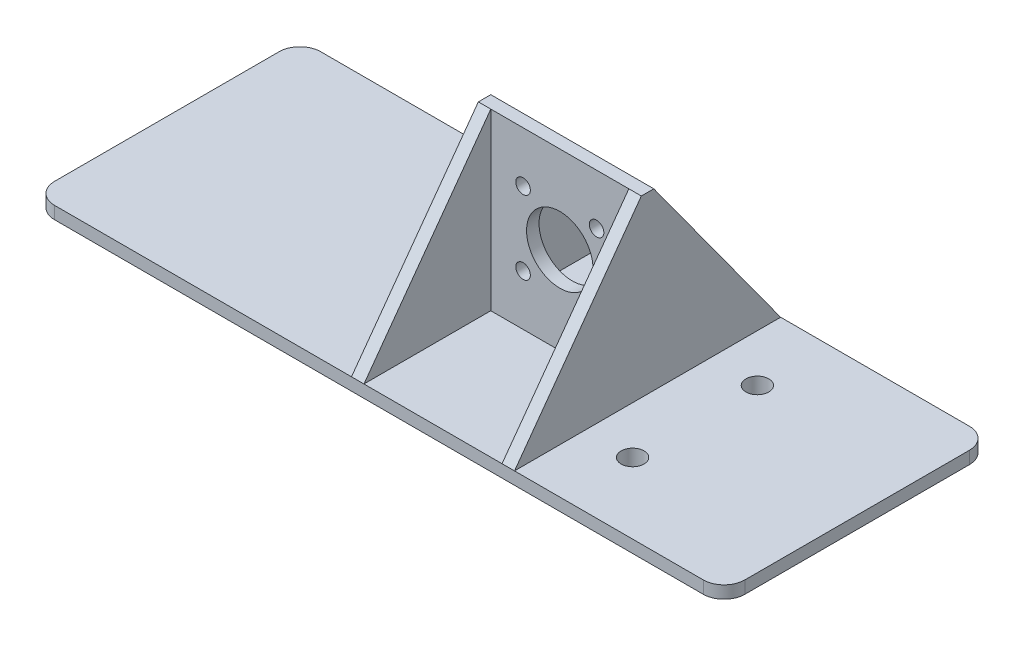
SolidWorks part; units mm, degrees
material "ABS PC"
ref_plane "Front Plane" through (0, 0, 0) normal (0, 0, 1) x (1, 0, 0)
ref_plane "Top Plane" through (0, 0, 0) normal (0, 1, 0) x (1, 0, 0)
ref_plane "Right Plane" through (0, 0, 0) normal (1, 0, 0) x (0, 0, -1)
sketch "Sketch1" plane through (0, 0, 0) normal (0, 1, 0) x (1, 0, 0)
  line L1 (78, 32) -> (-78, 32)
  line L2 (83, 27) -> (83, -27)
  line L3 (78, -32) -> (-78, -32)
  line L4 (-83, 27) -> (-83, -27)
  line L5 (83, 32) -> (-83, -32) construction
  line L6 (83, -32) -> (-83, 32) construction
  arc A0 (78, 32) -> (83, 27) centre (78, 27) cw
  arc A1 (83, -27) -> (78, -32) centre (78, -27) cw
  arc A2 (-78, -32) -> (-83, -27) centre (-78, -27) cw
  arc A3 (-78, 32) -> (-83, 27) centre (-78, 27) ccw
  point P0 (0, 0)
  dimension "D1" = 5
  dimension "D2" = 166
  dimension "D3" = 64
extrude "Boss-Extrude1" add sketch "Sketch1" along normal blind 3
sketch "Sketch2" plane through (0, 3, 0) normal (0, 1, 0) x (1, 0, 0)
  line L0 (-83, 0) -> (83, 0) construction
  line L1 (-83, 27) -> (-83, -27) construction
  line L2 (83, -27) -> (83, 27) construction
  circle A0 centre (44, -15) radius 2.75
  circle A1 centre (44, 15) radius 2.75
  circle A2 centre (-18, 0) radius 2.75
  dimension "D1" = 30
  dimension "D3" = 5.5
  dimension "D4" = 62
  dimension "D2" = 127
extrude "Cut-Extrude1" cut sketch "Sketch2" against normal through all
sketch "Sketch3" plane through (0, 3, 0) normal (0, 1, 0) x (1, 0, 0)
  line L0 (-78, -32) -> (78, -32) construction
  line L1 (-6.6, 32) -> (32.6, 32) construction
  line L2 (-6.6, 0) -> (-6.6, -32) construction
  line L3 (-6.6, -32) -> (32.6, -32) construction
  line L4 (32.6, -15) -> (32.6, -32) construction
  line L5 (78, 32) -> (-78, 32) construction
  line L6 (44, -15) -> (32.6, -15) construction
  line L7 (-18, 0) -> (-6.6, 0) construction
  line L8 (-6.6, 32) -> (-6.6, 0) construction
  line L9 (32.6, 32) -> (32.6, -15) construction
  line L11 (-6.6, 1.5) -> (32.6, 1.5)
  line L12 (-6.6, 1.5) -> (-6.6, -1.5)
  line L13 (-6.6, -1.5) -> (32.6, -1.5)
  line L14 (32.6, 1.5) -> (32.6, -1.5)
  point P18 (14.0261, -1.5)
  point P19 (-6.6, 0)
  point P20 (0, 0)
  dimension "D1" = 11.4
  dimension "D2" = 3
extrude "Boss-Extrude2" add sketch "Sketch3" along normal blind 42
sketch "Sketch6" plane through (0, 0, -1.5) normal (0, 0, -1) x (-1, 0, 0)
  line L0 (-13, 45) -> (-13, 3) construction
  line L1 (-32.6, 45) -> (6.6, 45) construction
  line L2 (-32.6, 3) -> (6.6, 3) construction
  line L3 (-13, 24) -> (-4.1612, 15.1612) construction
  line L4 (-32.6, 45) -> (-32.6, 3) construction
  line L5 (-32.6, 24) -> (6.6, 24) construction
  line L6 (6.6, 45) -> (6.6, 3) construction
  circle A0 centre (-13, 24) radius 8
  circle A1 centre (-4.1612, 15.1612) radius 1.75
  circle A2 centre (-21.8388, 15.1612) radius 1.75
  circle A3 centre (-21.8388, 32.8388) radius 1.75
  circle A4 centre (-4.1612, 32.8388) radius 1.75
  dimension "D1" = 16
  dimension "D3" = 3.5
  dimension "D2" = 12.5
  dimension "D4" = 45
extrude "Cut-Extrude2" cut sketch "Sketch6" against normal through all both
sketch "Sketch7" plane through (0, 0, -1.5) normal (0, 0, -1) x (-1, 0, 0)
  line L0 (-32.6, 3) -> (6.6, 3) construction
  line L1 (-32.6, 45) -> (-29.6, 45)
  line L2 (-32.6, 45) -> (-32.6, 3)
  line L3 (-32.6, 3) -> (-29.6, 3)
  line L4 (-29.6, 45) -> (-29.6, 3)
  line L5 (-78, 3) -> (78, 3) construction
  line L6 (6.6, 45) -> (3.6, 45)
  line L7 (6.6, 45) -> (6.6, 3)
  line L8 (6.6, 3) -> (3.6, 3)
  line L9 (3.6, 45) -> (3.6, 3)
  dimension "D1" = 3
  dimension "D2" = 3
extrude "Boss-Extrude3" add sketch "Sketch7" along normal blind 30.5 and the other way blind 33.5
sketch "Sketch8" plane through (-6.6, 0, 0) normal (-1, 0, 0) x (0, 0, 1)
  line L0 (-1.5, 45) -> (-32, 3)
  line L1 (-32, 3) -> (-32, 45)
  line L2 (-32, 45) -> (-1.5, 45)
  line L3 (1.5, 45) -> (32, 3)
  line L4 (32, 3) -> (32, 45)
  line L5 (32, 45) -> (1.5, 45)
extrude "Cut-Extrude5" cut sketch "Sketch8" against normal through all both
sketch "Sketch9" plane through (0, 0, 0) normal (0, -1, 0) x (1, 0, 0)
  circle A0 centre (-18, 0) radius 4.75
  circle A1 centre (44, -15) radius 4.75
  circle A2 centre (44, 15) radius 4.75
  circle A3 centre (-18, 0) radius 2.75
  circle A4 centre (44, 15) radius 2.75
  circle A5 centre (44, -15) radius 2.75
  dimension "D1" = 9.5
  dimension "D2" = 9.5
  dimension "D3" = 9.5
extrude "Boss-Extrude4" add sketch "Sketch9" along normal blind 4.5
